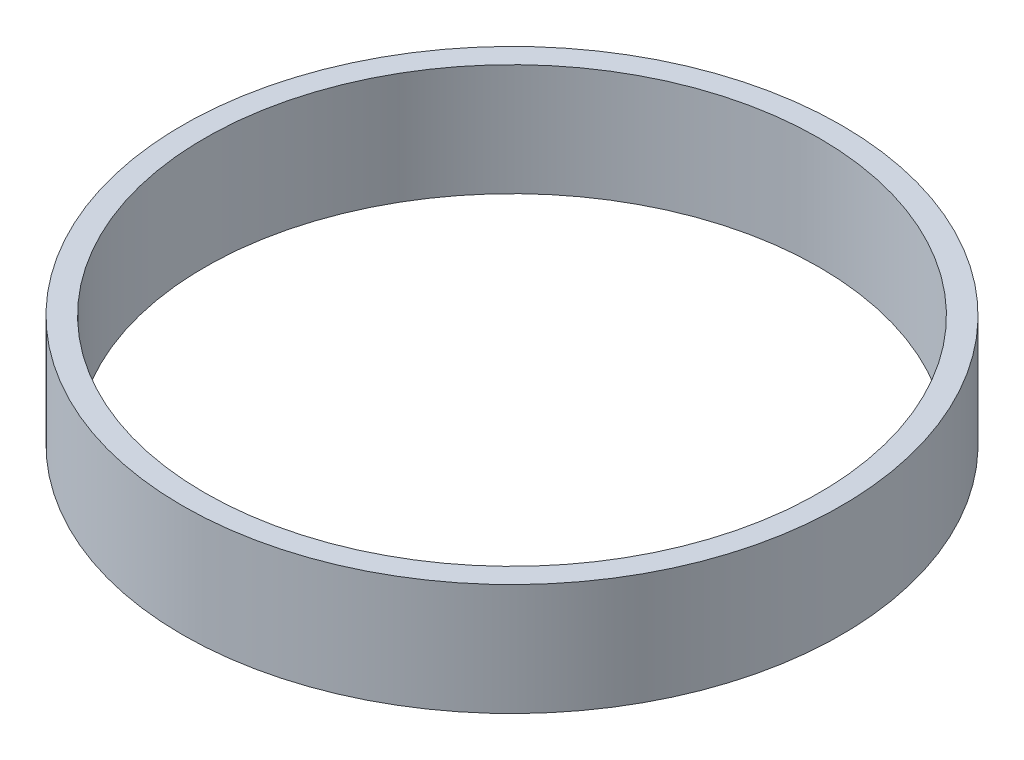
SolidWorks part; units mm, degrees
material "1060 Сплав"
ref_plane "Front Plane" through (0, 0, 0) normal (0, 0, 1) x (1, 0, 0)
ref_plane "Top Plane" through (0, 0, 0) normal (0, 1, 0) x (1, 0, 0)
ref_plane "Right Plane" through (0, 0, 0) normal (1, 0, 0) x (0, 0, -1)
sketch "Эскиз1" plane through (0, 0, 0) normal (0, 1, 0) x (1, 0, 0)
  circle A0 centre (0, 0) radius 27.5
  circle A1 centre (0, 0) radius 29.5
  dimension "D1" = 59
  dimension "D2" = 55
extrude "Бобышка-Вытянуть1" add sketch "Эскиз1" along normal blind 10
